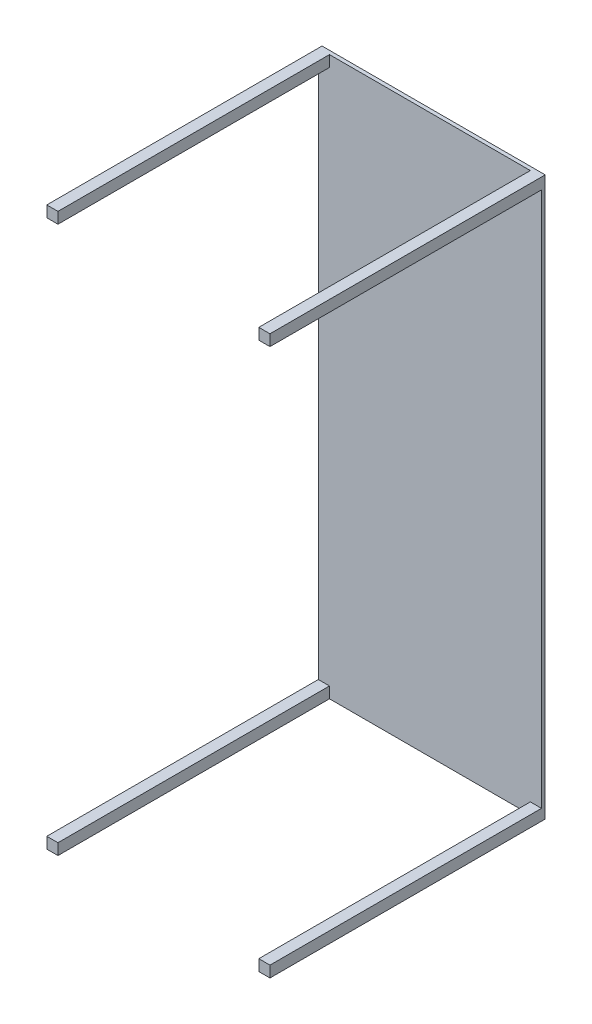
SolidWorks part; units mm, degrees
ref_plane "Front Plane" through (0, 0, 0) normal (0, 0, 1) x (1, 0, 0)
ref_plane "Top Plane" through (0, 0, 0) normal (0, 1, 0) x (1, 0, 0)
ref_plane "Right Plane" through (0, 0, 0) normal (1, 0, 0) x (0, 0, -1)
sketch "Sketch1" plane through (0, 0, 0) normal (0, 0, 1) x (1, 0, 0)
  line L1 (-300, 750) -> (300, 750)
  line L2 (-300, 750) -> (-300, -750)
  line L3 (-300, -750) -> (300, -750)
  line L4 (300, 750) -> (300, -750)
  line L5 (-300, 750) -> (300, -750) construction
  line L6 (-300, -750) -> (300, 750) construction
  point P0 (0, 0)
  dimension "D1" = 600
  dimension "D2" = 1500
extrude "Boss-Extrude1" add sketch "Sketch1" along normal blind 10
sketch "Sketch2" plane through (0, 0, 10) normal (0, 0, 1) x (1, 0, 0)
  line L0 (300, 750) -> (-300, 750) construction
  line L1 (-300, 750) -> (-270, 750)
  line L2 (-300, 750) -> (-300, 720)
  line L3 (-300, 720) -> (-270, 720)
  line L4 (-270, 750) -> (-270, 720)
  line L5 (-300, 750) -> (-300, -750) construction
  line L6 (270, 750) -> (300, 750)
  line L7 (270, 750) -> (270, 720)
  line L8 (270, 720) -> (300, 720)
  line L9 (300, 750) -> (300, 720)
  line L10 (270, -720) -> (300, -720)
  line L11 (270, -720) -> (270, -750)
  line L12 (270, -750) -> (300, -750)
  line L13 (300, -720) -> (300, -750)
  line L14 (-300, -720) -> (-270, -720)
  line L15 (-300, -720) -> (-300, -750)
  line L16 (-300, -750) -> (-270, -750)
  line L17 (-270, -720) -> (-270, -750)
  dimension "D1" = 30
  dimension "D2" = 30
  dimension "D3" = 30
  dimension "D4" = 30
  dimension "D5" = 30
  dimension "D6" = 30
  dimension "D7" = 30
  dimension "D8" = 30
extrude "Boss-Extrude2" add sketch "Sketch2" along normal blind 730
